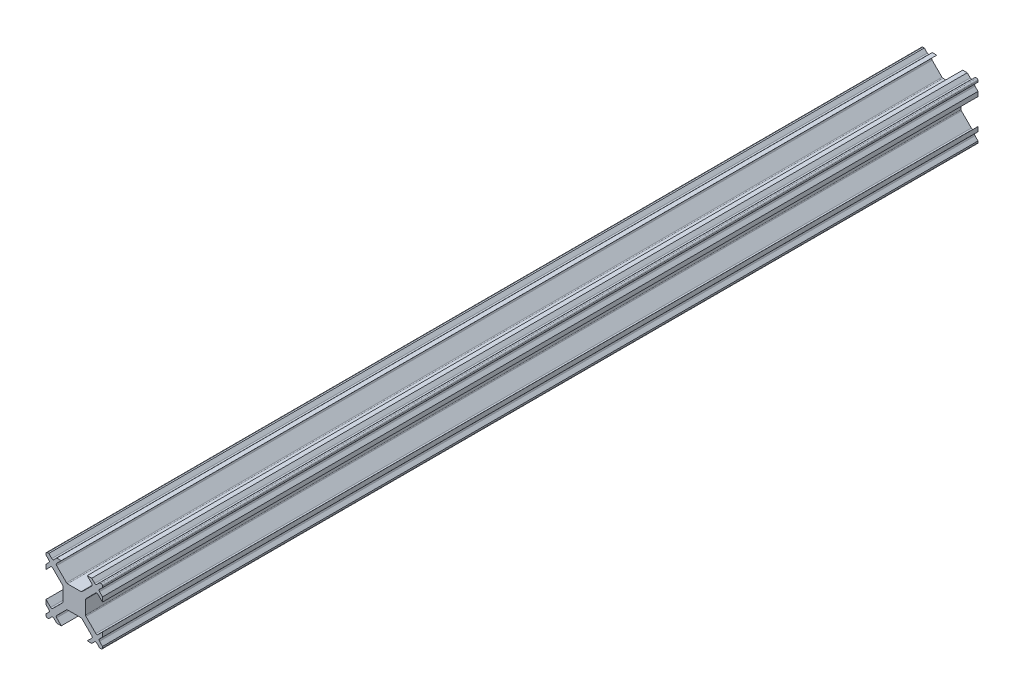
SolidWorks part; units mm, degrees
ref_plane "Front Plane" through (0, 0, 0) normal (0, 0, 1) x (1, 0, 0)
ref_plane "Top Plane" through (0, 0, 0) normal (0, 1, 0) x (1, 0, 0)
ref_plane "Right Plane" through (0, 0, 0) normal (1, 0, 0) x (0, 0, -1)
sketch "Sketch2" plane through (0, 0, 0) normal (0, 0, 1) x (1, 0, 0)
  line L0 (-1.3661, 2.0732) -> (-3.1161, 3.8232)
  line L1 (-3.1161, 4.1768) -> (-2.2929, 5)
  line L2 (-2.2929, 5) -> (-3.095, 5)
  line L3 (-3.095, 5) -> (-3.6232, 4.4718)
  line L4 (-3.9768, 4.4718) -> (-4.505, 5)
  line L5 (-4.505, 5) -> (-4.75, 5)
  line L51 (0, 2) -> (-1.1893, 2)
  line L52 (-2.6939, 5) -> (-3.847, 3.847) construction
  line L53 (0, 0) -> (0, 2)
  line L54 (0, 0) -> (-4.9268, 4.9268)
  arc A0 (-3.1161, 4.1768) -> (-3.1161, 3.8232) centre (-2.9393, 4) ccw
  arc A1 (-3.9768, 4.4718) -> (-3.6232, 4.4718) centre (-3.8, 4.6485) ccw
  arc A2 (-4.75, 5) -> (-4.9268, 4.9268) centre (-4.75, 4.75) ccw
  arc A27 (-1.3661, 2.0732) -> (-1.1893, 2) centre (-1.1893, 2.25) ccw
  point P115 (-3.2929, 4)
  point P116 (-3.8, 4.295)
  dimension "D4" = 0.25
  dimension "D1" = 2
  dimension "D2" = 45
  dimension "D3" = 0.5
  dimension "D5" = 5
  dimension "D6" = 0.35
  dimension "D7" = 4
  dimension "D8" = 3.8
extrude "Boss-Extrude1" add sketch "Sketch2" along normal blind 155
mirror "Mirror1" about plane through (0, 0, 155) normal (0.7071, 0.7071, 0) of "Boss-Extrude1"
pattern_circular "CirPattern4" count 4 over 360 about axis through (0, 0, 0) along (0, 0, 1) of "Mirror1", "Boss-Extrude1"
